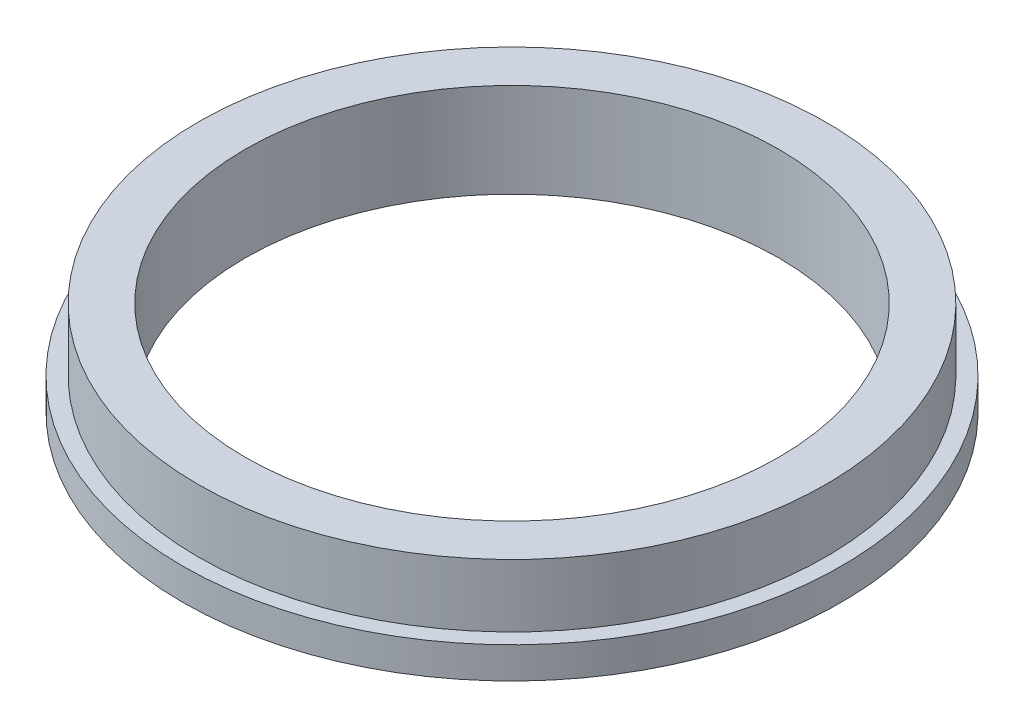
SolidWorks part; units mm, degrees
ref_plane "Front Plane" through (0, 0, 0) normal (0, 0, 1) x (1, 0, 0)
ref_plane "Top Plane" through (0, 0, 0) normal (0, 1, 0) x (1, 0, 0)
ref_plane "Right Plane" through (0, 0, 0) normal (1, 0, 0) x (0, 0, -1)
sketch "Sketch1" plane through (0, 0, 0) normal (0, 1, 0) x (1, 0, 0)
  circle A0 centre (0, 0) radius 52.5
  dimension "D1" = 105
extrude "Boss-Extrude1" add sketch "Sketch1" along normal blind 5
sketch "Sketch2" plane through (0, 5, 0) normal (0, 1, 0) x (1, 0, 0)
  circle A1 centre (0, 0) radius 50
  circle A2 centre (0, 0) radius 42.5
  dimension "D1" = 100
  dimension "D2" = 85
extrude "Boss-Extrude2" add sketch "Sketch2" along normal blind 10
sketch "Sketch3" plane through (0, 5, 0) normal (0, 1, 0) x (1, 0, 0)
  circle A0 centre (0, 0) radius 42.5
extrude "Cut-Extrude1" cut sketch "Sketch3" against normal through all
